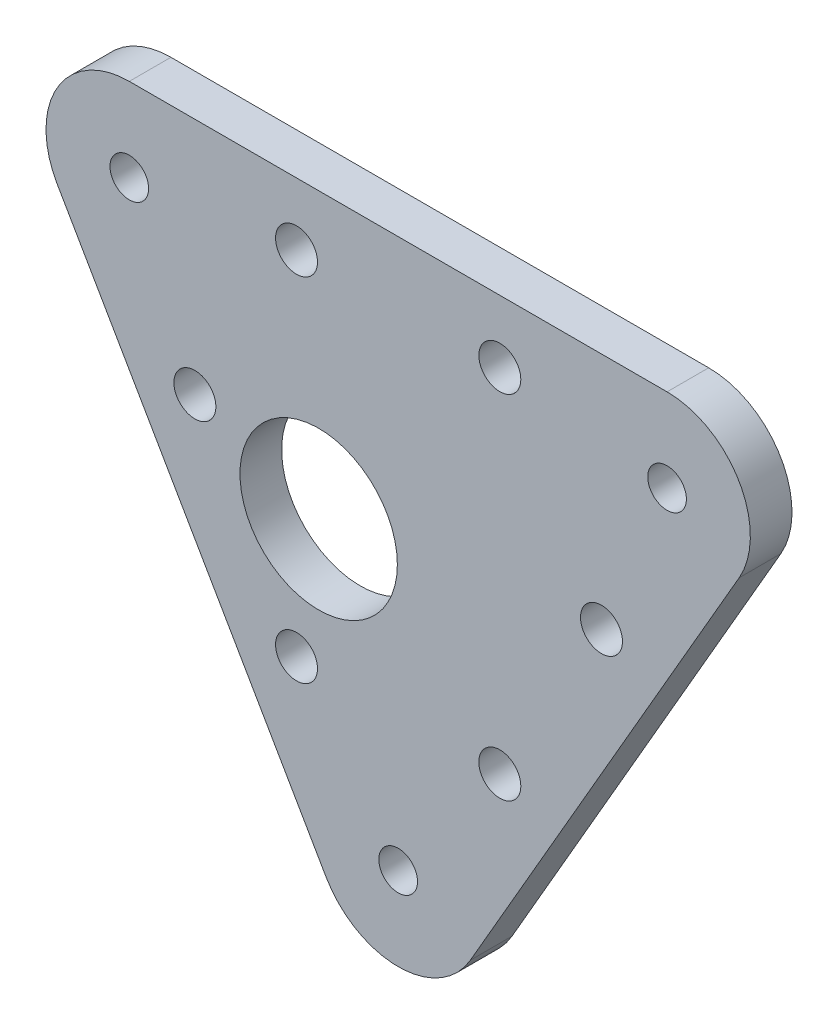
SolidWorks part; units mm, degrees
material "Acrylic (Medium-high impact)"
ref_plane "Front Plane" through (0, 0, 0) normal (0, 0, 1) x (1, 0, 0)
ref_plane "Top Plane" through (0, 0, 0) normal (0, 1, 0) x (1, 0, 0)
ref_plane "Right Plane" through (0, 0, 0) normal (1, 0, 0) x (0, 0, -1)
sketch "Sketch1" plane through (0, 0, 0) normal (0, 0, 1) x (1, 0, 0)
  line L0 (-6.0622, -3.5) -> (4.1556, -3.5) construction
  line L1 (0, 0) -> (-6.0622, -3.5) construction
  line L2 (-31.4989, 18.1859) -> (0, -36.3718)
  line L3 (-31.4989, 18.1859) -> (31.4989, 18.1859)
  line L4 (31.4989, 18.1859) -> (0, -36.3718)
  line L7 (-7.75, -13.4234) -> (7.75, -13.4234) construction
  line L8 (7.75, -13.4234) -> (15.5, 0) construction
  line L9 (15.5, 0) -> (7.75, 13.4234) construction
  line L10 (7.75, 13.4234) -> (-7.75, 13.4234) construction
  line L11 (-7.75, 13.4234) -> (-15.5, 0) construction
  line L12 (-15.5, 0) -> (-7.75, -13.4234) construction
  circle A0 centre (0, 0) radius 13.4234 construction
  circle A1 centre (-6.0622, -3.5) radius 6
  point P0 (0, 0)
  dimension "D5" = 12
  dimension "D1" = 15.5
  dimension "D2" = 30
  dimension "D3" = 4.7625
  dimension "D4" = 7
  dimension "D6" = 4.7625
  dimension "D7" = 4.7625
extrude "Boss-Extrude1" add sketch "Sketch1" along normal blind 3.175
hole_wizard "M3 Clearance Hole1" positions "Sketch3" profile "Sketch2" hole size "M3" standard "Ansi Metric" end condition through all
sketch "Sketch3" plane through (-27.3884, 15.2428, 3.175) normal (0, 0, 1) x (1, 0, 0)
  line L0 (42.8884, -15.2428) -> (35.1384, -1.8194) construction
  point P0 (19.6384, -1.8194)
  point P1 (35.1384, -1.8194)
  point P4 (42.8884, -15.2428)
  point P13 (11.8884, -15.2428)
  point P16 (19.6384, -28.6662)
  point P19 (35.1384, -28.6662)
sketch "Sketch2" plane through (-7.75, 13.4234, 3.175) normal (1, 0, 0) x (0, -1, 0)
  line L0 (0, 0) -> (0, 3.175)
  line L1 (0, 3.175) -> (1.6, 3.175)
  line L2 (1.6, 3.175) -> (1.6, 0)
  line L5 (1.6, 0) -> (0, 0)
  line L11 (0, -6.35) -> (0, 107.95) construction
  dimension "Thru Hole Dia." = 3.2
  dimension "Thru Hole Depth" = 3.175
fillet "Fillet1" radius 6.35 3 edges at (0, -36.3718, 1.5875) (31.4989, 18.1859, 1.5875) (-31.4989, 18.1859, 1.5875)
hole_wizard "#4 Clearance Hole1" positions "Sketch7" profile "Sketch6" hole size "#4" standard "Ansi Inch"
sketch "Sketch7" plane through (-21.0851, 23.0045, 3.175) normal (0, 0, 1) x (1, 0, 0)
  point P0 (0.5848, -11.1686)
  point P5 (41.5855, -11.1686)
  point P9 (21.0851, -46.6763)
sketch "Sketch6" plane through (-20.5004, 11.8359, 3.175) normal (1, 0, 0) x (0, -1, 0)
  line L0 (0, 0) -> (0, 4.1872)
  line L1 (0, 4.1872) -> (1.4732, 3.302)
  line L2 (1.4732, 3.302) -> (1.4732, 0)
  line L5 (1.4732, 0) -> (0, 0)
  line L10 (0, 4.1872) -> (-1.4732, 3.302) construction
  line L11 (0, -6.35) -> (0, 107.95) construction
  dimension "Hole Dia." = 2.9464
  dimension "Hole Depth" = 3.302
  dimension "Drill Angle" = 118
